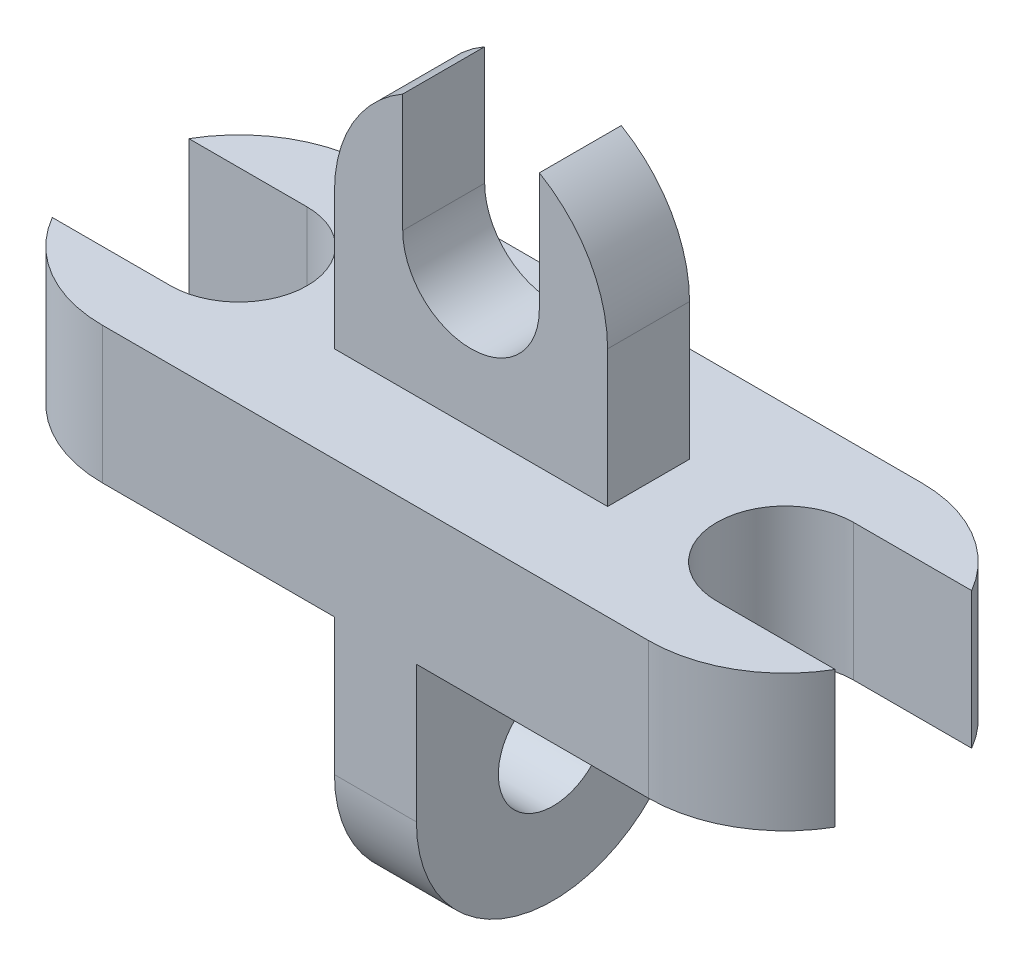
SolidWorks part; units mm, degrees
ref_plane "Front Plane" through (0, 0, 0) normal (0, 0, 1) x (1, 0, 0)
ref_plane "Top Plane" through (0, 0, 0) normal (0, 1, 0) x (1, 0, 0)
ref_plane "Right Plane" through (0, 0, 0) normal (1, 0, 0) x (0, 0, -1)
sketch "Sketch1" plane through (0, 0, 0) normal (0, 1, 0) x (1, 0, 0)
  line L3 (100, 50) -> (-100, 50)
  line L4 (100, -50) -> (-100, -50)
  line L5 (-100, -25) -> (-143.3013, -25)
  line L6 (100, 25) -> (143.3013, 25)
  line L7 (100, -25) -> (143.3013, -25)
  line L8 (-100, 25) -> (-143.3013, 25)
  arc A0 (100, 25) -> (100, -25) centre (100, 0) ccw
  arc A1 (100, -50) -> (143.3013, -25) centre (100, 0) ccw
  arc A2 (143.3013, 25) -> (100, 50) centre (100, 0) ccw
  arc A3 (-143.3013, 25) -> (-100, 50) centre (-100, 0) cw
  arc A4 (-100, -50) -> (-143.3013, -25) centre (-100, 0) cw
  arc A5 (-100, 25) -> (-100, -25) centre (-100, 0) cw
  point P13 (0, 50)
  point P23 (0, -50)
  dimension "D2" = 100
  dimension "D3" = 50
  dimension "D4" = 50
  dimension "D5" = 25
  dimension "D1" = 200
extrude "Boss-Extrude1" add sketch "Sketch1" along normal mid plane 50
sketch "Sketch2" plane through (0, 25, 0) normal (0, 1, 0) x (1, 0, 0)
  line L1 (-50, -15) -> (50, -15)
  line L2 (-50, -15) -> (-50, 15)
  line L3 (-50, 15) -> (50, 15)
  line L4 (50, -15) -> (50, 15)
  line L5 (-50, -15) -> (50, 15) construction
  line L6 (-50, 15) -> (50, -15) construction
  point P0 (0, 0)
  dimension "D1" = 100
  dimension "D2" = 30
extrude "Boss-Extrude3" add sketch "Sketch2" along normal blind 150
sketch "Sketch4" plane through (0, 0, 15) normal (0, 0, 1) x (1, 0, 0)
  line L1 (-25, 75) -> (-25, 118.3013)
  line L2 (50, 175) -> (50, 25) construction
  line L3 (-50, 175) -> (-50, 25) construction
  line L4 (50, 175) -> (50, 75)
  line L5 (-50, 175) -> (-50, 75)
  line L6 (-50, 175) -> (50, 175) construction
  line L7 (-50, 175) -> (50, 175)
  line L8 (25, 75) -> (25, 118.3013)
  arc A0 (50, 75) -> (25, 118.3013) centre (0, 75) ccw
  arc A1 (-25, 75) -> (25, 75) centre (0, 75) ccw
  arc A2 (-25, 118.3013) -> (-50, 75) centre (0, 75) ccw
  dimension "D1" = 100
  dimension "D2" = 50
extrude "Cut-Extrude1" cut sketch "Sketch4" against normal blind 150
sketch "Sketch6" plane through (0, 0, 0) normal (1, 0, 0) x (0, 0, -1)
  line L0 (-149.9435, -74.9987) -> (-50, -74.9987) construction
  line L1 (0, 163.4816) -> (0, -25) construction
  line L2 (15, 118.3013) -> (-15, 118.3013) construction
  line L3 (-50, -74.9987) -> (-50, -25)
  line L4 (50, -74.9987) -> (50, -25)
  line L5 (-25, -25) -> (25, -25) construction
  line L6 (25, -25) -> (50, -25) construction
  line L7 (-50, -25) -> (-25, -25) construction
  line L8 (-25, -25) -> (25, -25)
  line L9 (25, -25) -> (50, -25)
  line L10 (-50, -25) -> (-25, -25)
  line L11 (50, -74.9987) -> (126.2024, -74.9987) construction
  arc A0 (-50, -74.9987) -> (50, -74.9987) centre (0, -74.9987) ccw
  arc A1 (0.3564, -25) -> (-0.3564, -25) centre (0, -74.9987) ccw
  dimension "D1" = 193.3
extrude "Boss-Extrude4" add sketch "Sketch6" along normal mid plane 30 contours A0 L4 L9 L8 L10 L3
sketch "Sketch7" plane through (15, 0, 0) normal (1, 0, 0) x (0, 0, -1)
  circle A0 centre (0, -74.9987) radius 20
  dimension "D1" = 40
extrude "Cut-Extrude2" cut sketch "Sketch7" against normal blind 30
